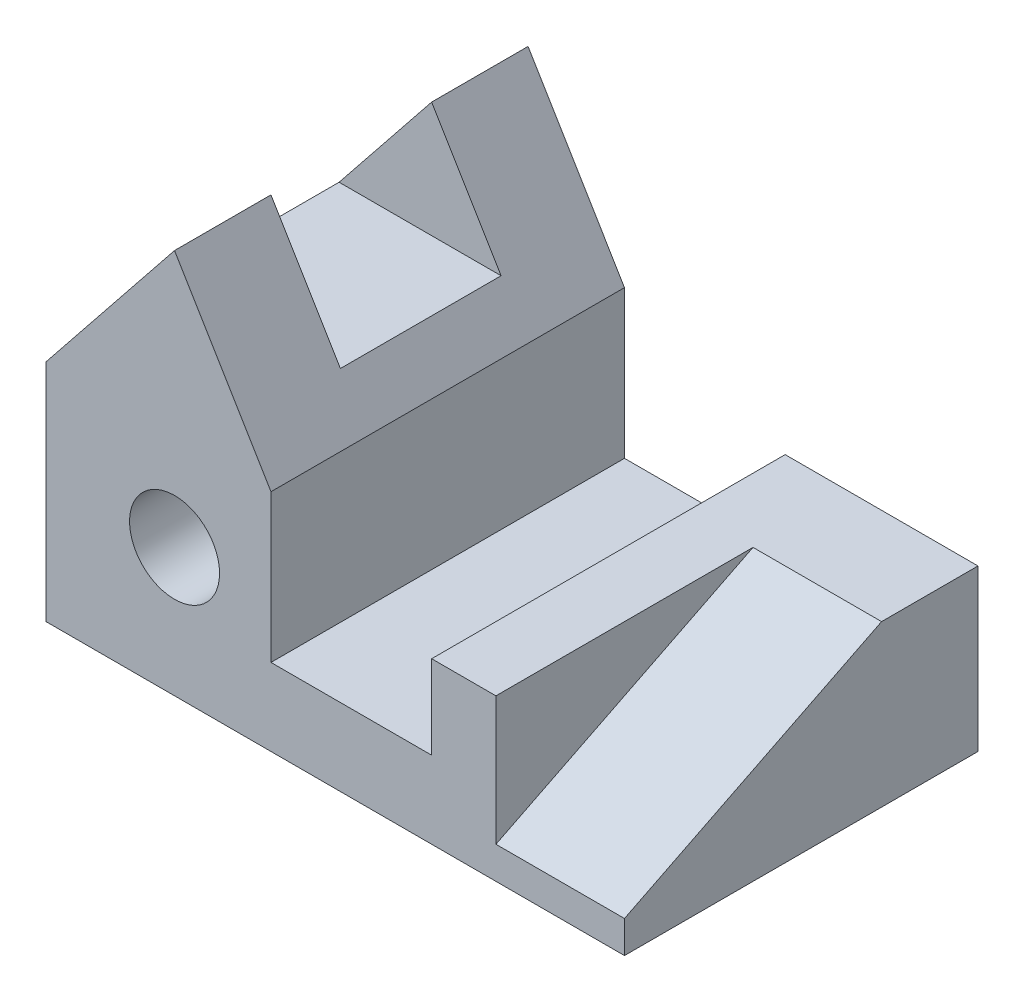
SolidWorks part; units mm, degrees
ref_plane "Front Plane" through (0, 0, 0) normal (0, 0, 1) x (1, 0, 0)
ref_plane "Top Plane" through (0, 0, 0) normal (0, 1, 0) x (1, 0, 0)
ref_plane "Right Plane" through (0, 0, 0) normal (1, 0, 0) x (0, 0, -1)
sketch "Sketch2" plane through (0, 0, 0) normal (0, 0, 1) x (1, 0, 0)
  line L0 (0, 0) -> (0, 35)
  line L1 (0, 35) -> (20, 60)
  line L2 (20, 60) -> (35, 35)
  line L3 (35, 35) -> (35, 12)
  line L4 (35, 12) -> (60, 12)
  line L5 (60, 12) -> (60, 25)
  line L6 (60, 25) -> (90, 25)
  line L7 (90, 25) -> (90, 0)
  line L8 (90, 0) -> (0, 0)
  line L9 (70, 25) -> (70, 0) construction
  circle A0 centre (20, 20) radius 7
  point P12 (0, 0)
  dimension "D11" = 14
  dimension "D1" = 90
  dimension "D2" = 35
  dimension "D3" = 12
  dimension "D4" = 25
  dimension "D5" = 30
  dimension "D6" = 10
  dimension "D7" = 60
  dimension "D8" = 20
  dimension "D9" = 25
  dimension "D10" = 20
extrude "Boss-Extrude1" add sketch "Sketch2" along normal blind 55
sketch "Sketch3" plane through (90, 0, 0) normal (1, 0, 0) x (0, 0, -1)
  line L0 (-55, 5) -> (-15, 25)
  line L1 (-55, 0) -> (-55, 25) construction
  line L2 (-55, 25) -> (0, 25) construction
  dimension "D1" = 5
  dimension "D2" = 15
extrude "Cut-Extrude1" cut sketch "Sketch3" against normal blind 20 and the other way through all
sketch "Sketch5" plane through (0, 0, 0) normal (-1, 0, 0) x (0, 0, 1)
  line L0 (55, 60) -> (0, 60) construction
  line L1 (15, 60) -> (40, 60)
  line L2 (15, 60) -> (15, 42)
  line L3 (15, 42) -> (40, 42)
  line L4 (40, 60) -> (40, 42)
  line L5 (0, 60) -> (0, 35) construction
  line L6 (55, 60) -> (55, 35) construction
  dimension "D1" = 18
  dimension "D2" = 15
  dimension "D3" = 15
extrude "Cut-Extrude2" cut sketch "Sketch5" against normal through all
